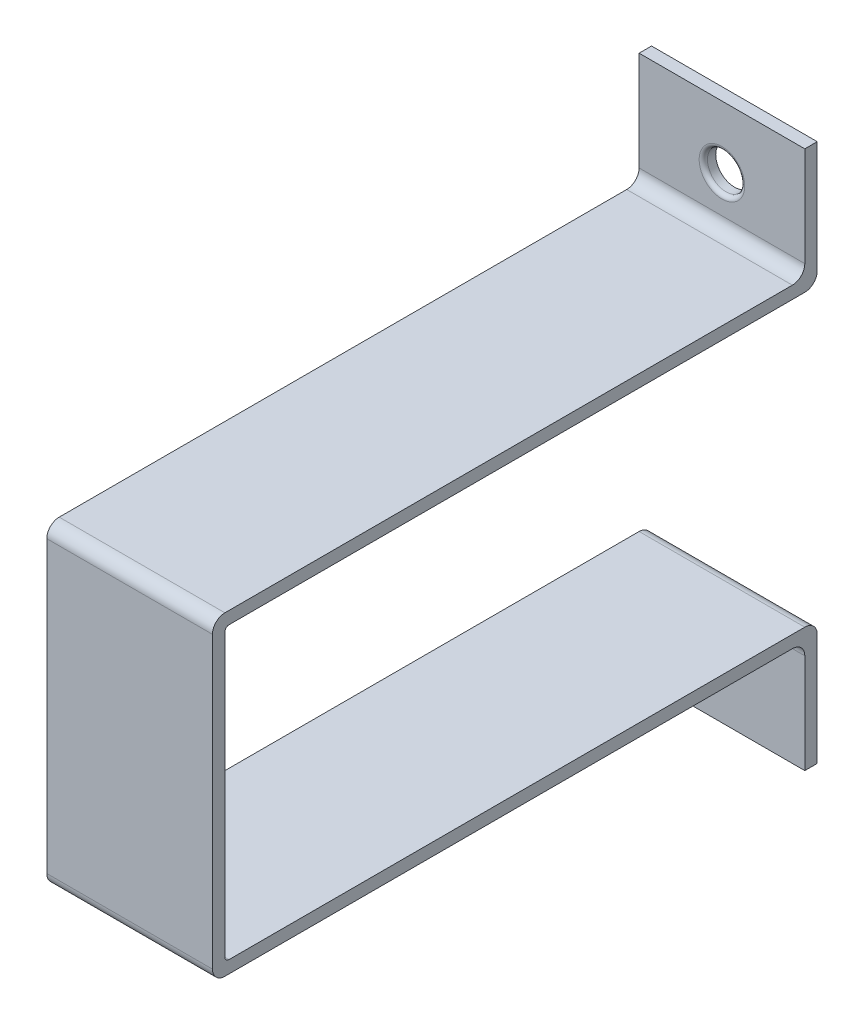
SolidWorks part; units mm, degrees
ref_plane "Plan de face" through (0, 0, 0) normal (0, 0, 1) x (1, 0, 0)
ref_plane "Plan de dessus" through (0, 0, 0) normal (0, 1, 0) x (1, 0, 0)
ref_plane "Plan de droite" through (0, 0, 0) normal (1, 0, 0) x (0, 0, -1)
sketch "Esquisse1" plane through (0, 0, 0) normal (0, 0, 1) x (1, 0, 0)
  line L1 (-20, 35) -> (20, 35)
  line L2 (-20, 35) -> (-20, -35)
  line L3 (-20, -35) -> (20, -35)
  line L4 (20, 35) -> (20, -35)
  point P4 (-20, 0)
  point P6 (0, 35)
  dimension "D1" = 40
  dimension "D2" = 70
extrude "Boss.-Extru.1" add sketch "Esquisse1" along normal blind 3
sketch "Esquisse4" plane through (0, 0, 3) normal (0, 0, 1) x (1, 0, 0)
  line L1 (-20, 35) -> (20, 35)
  line L2 (-20, 35) -> (-20, 38)
  line L3 (-20, 38) -> (20, 38)
  line L4 (20, 35) -> (20, 38)
  line L5 (-20, -35) -> (20, -35)
  line L6 (-20, -35) -> (-20, -38)
  line L7 (-20, -38) -> (20, -38)
  line L8 (20, -35) -> (20, -38)
  dimension "D1" = 3
  dimension "D2" = 3
ref_plane "Plan1" through (0, 0, -140) normal (0, 0, 1) x (1, 0, 0)
extrude "Boss.-Extru.3" add sketch "Esquisse4" against normal up to surface (143 mm away) up to plane "Plan1"
sketch "Esquisse5" plane through (0, 0, -140) normal (0, 0, -1) x (-1, 0, 0)
  line L1 (-20, 35) -> (20, 35)
  line L2 (-20, 35) -> (-20, 65)
  line L3 (-20, 65) -> (20, 65)
  line L4 (20, 35) -> (20, 65)
  line L5 (-20, -35) -> (20, -35)
  line L6 (-20, -35) -> (-20, -65)
  line L7 (-20, -65) -> (20, -65)
  line L8 (20, -35) -> (20, -65)
  dimension "D1" = 30
  dimension "D2" = 30
extrude "Boss.-Extru.4" add sketch "Esquisse5" along normal blind 3
sketch "Esquisse6" plane through (0, 0, -143) normal (0, 0, -1) x (-1, 0, 0)
  line L0 (-103.949, 0) -> (103.949, 0) construction
  circle A0 centre (0, 50) radius 4.5
  circle A1 centre (0, -50) radius 4.5
  point P2 (0, 0)
  dimension "D2" = 9
  dimension "D1" = 50
extrude "Enlèv. mat.-Extru.1" cut sketch "Esquisse6" against normal through all
fillet "Congé1" radius 1 2 edges at (0, -35, 0) (0, 35, 0)
fillet "Congé2" radius 3 2 edges at (0, 38, 3) (0, -38, 3)
fillet "Congé3" radius 3 2 edges at (0, -38, -140) (0, 38, -140)
fillet "Congé4" radius 3 2 edges at (0, -35, -143) (0, 35, -143)
fillet "Congé5" radius 1 2 edges at (-4.5, -50, -140) (4.5, 50, -140)
